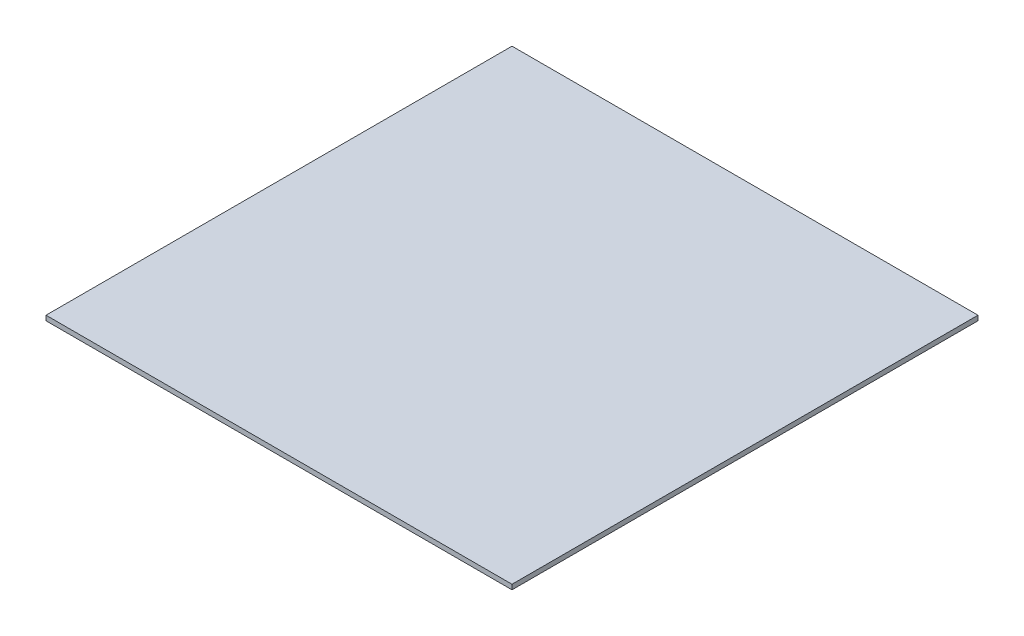
SolidWorks part; units mm, degrees
ref_plane "Front Plane" through (0, 0, 0) normal (0, 0, 1) x (1, 0, 0)
ref_plane "Top Plane" through (0, 0, 0) normal (0, 1, 0) x (1, 0, 0)
ref_plane "Right Plane" through (0, 0, 0) normal (1, 0, 0) x (0, 0, -1)
sketch "Sketch1" plane through (0, 0, 0) normal (0, 1, 0) x (1, 0, 0)
  line L0 (-152.4, 152.4) -> (-76.2, 76.2) construction
  line L1 (152.4, -152.4) -> (-152.4, -152.4)
  line L2 (152.4, -152.4) -> (152.4, 152.4)
  line L3 (152.4, 152.4) -> (-152.4, 152.4)
  line L4 (-152.4, -152.4) -> (-152.4, 152.4)
  line L5 (152.4, -152.4) -> (-152.4, 152.4) construction
  line L6 (152.4, 152.4) -> (-152.4, -152.4) construction
  line L7 (-152.4, -152.4) -> (-76.2, -76.2) construction
  line L8 (152.4, 152.4) -> (76.2, 76.2) construction
  line L9 (152.4, -152.4) -> (76.2, -76.2) construction
  point P0 (0, 0)
  point P9 (-76.2, 76.2)
  point P11 (-76.2, -76.2)
  point P14 (76.2, 76.2)
  point P15 (76.2, -76.2)
  dimension "Length" = 304.8
  dimension "Width" = 304.8
  dimension "Break Line 1" = 76.2
  dimension "Break Line 2" = 76.2
  dimension "Break Line 3" = 76.2
  dimension "Break Line 4" = 76.2
sketch "Sketch2" plane through (0, 0, 0) normal (1, 0, 0) x (0, 0, -1)
  line L0 (152.4, 1.5875) -> (152.4, -1.5875) construction
  point P2 (152.4, 0)
  dimension "Thickness" = 3.175
sketch "Sketch3" plane through (0, 0, 0) normal (0, 1, 0) x (1, 0, 0)
  line L1 (-152.4, 152.4) -> (152.4, 152.4)
  line L2 (-152.4, 152.4) -> (-152.4, -152.4)
  line L3 (-152.4, -152.4) -> (152.4, -152.4)
  line L4 (152.4, 152.4) -> (152.4, -152.4)
extrude "Boss-Extrude1" add sketch "Sketch3" against normal up to vertex (1.5875 mm away) and the other way up to vertex (1.5875 mm away) up to point (0, -1.5875, -152.4) other way up to point (0, 1.5875, -152.4)
equation "\"Break Line 1@Sketch1\"=\"Length@Sketch1\"*1/4"
equation "\"Break Line 2@Sketch1\"=\"Width@Sketch1\" * 1/4"
equation "\"Break Line 3@Sketch1\"=\"Break Line 1@Sketch1\""
equation "\"Break Line 4@Sketch1\" = \"Break Line 2@Sketch1\""
